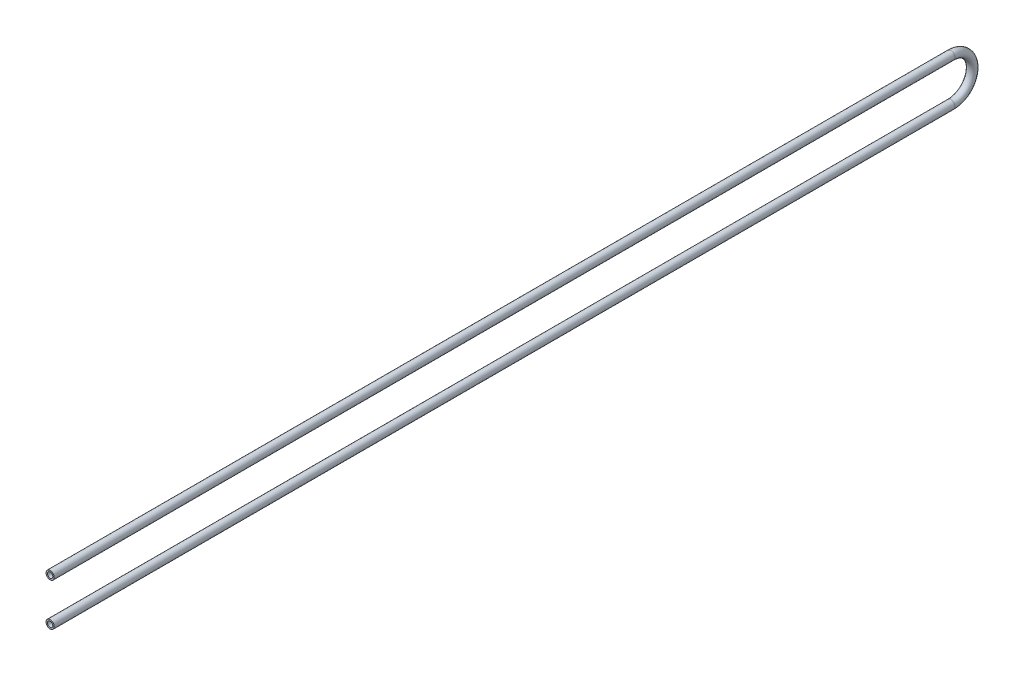
SolidWorks part; units mm, degrees
material "AISI 304"
ref_plane "Front Plane" through (0, 0, 0) normal (0, 0, 1) x (1, 0, 0)
ref_plane "Top Plane" through (0, 0, 0) normal (0, 1, 0) x (1, 0, 0)
ref_plane "Right Plane" through (0, 0, 0) normal (1, 0, 0) x (0, 0, -1)
sketch "Sketch1" plane through (0, 0, 0) normal (1, 0, 0) x (0, 0, -1)
  line L0 (0, 0) -> (0, 55) construction
  line L1 (0, 55) -> (2325, 55)
  line L2 (2325, -55) -> (0, -55)
  arc A0 (2325, 55) -> (2325, -55) centre (2325, 0) cw
  dimension "D1" = 55
  dimension "D2" = 2325
sketch "Sketch2" plane through (0, 0, 0) normal (0, 0, 1) x (1, 0, 0)
  circle A0 centre (0, 55) radius 10.65
  circle A2 centre (0, 55) radius 6.92
  dimension "D1" = 13.84
  dimension "D2" = 21.3
sweep "Sweep1" add profiles "Sketch2" path "Sketch1"
